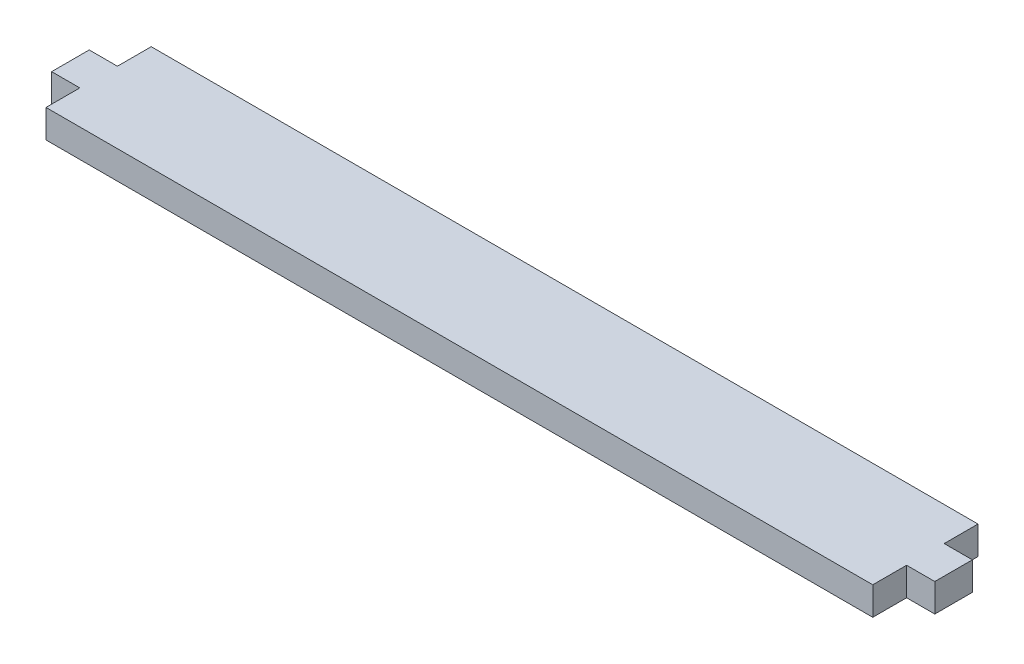
SolidWorks part; units mm, degrees
ref_plane "Front Plane" through (0, 0, 0) normal (0, 0, 1) x (1, 0, 0)
ref_plane "Top Plane" through (0, 0, 0) normal (0, 1, 0) x (1, 0, 0)
ref_plane "Right Plane" through (0, 0, 0) normal (1, 0, 0) x (0, 0, -1)
sketch "Sketch1" plane through (0, 0, 0) normal (0, 1, 0) x (1, 0, 0)
  line L1 (139.7, -17.78) -> (-139.7, -17.78)
  line L2 (139.7, -17.78) -> (139.7, 17.78)
  line L3 (139.7, 17.78) -> (-139.7, 17.78)
  line L4 (-139.7, -17.78) -> (-139.7, 17.78)
  line L5 (139.7, -17.78) -> (-139.7, 17.78) construction
  line L6 (139.7, 17.78) -> (-139.7, -17.78) construction
  point P0 (0, 0)
  dimension "D1" = 279.4
  dimension "D2" = 35.56
extrude "Boss-Extrude1" add sketch "Sketch1" along normal blind 9.525
sketch "Sketch2" plane through (139.7, 0, 0) normal (1, 0, 0) x (0, 0, -1)
  line L0 (-17.78, 0) -> (17.78, 0) construction
  line L1 (-6.35, 0) -> (6.35, 0)
  line L2 (-6.35, 0) -> (-6.35, 9.525)
  line L3 (-6.35, 9.525) -> (6.35, 9.525)
  line L4 (6.35, 0) -> (6.35, 9.525)
  line L5 (-17.78, 9.525) -> (17.78, 9.525) construction
  line L6 (-17.78, 9.525) -> (-17.78, 0) construction
  dimension "D1" = 12.7
  dimension "D2" = 11.43
extrude "Boss-Extrude2" add sketch "Sketch2" along normal blind 9.525
mirror "Mirror1" about plane through (0, 0, 0) normal (1, 0, 0) of "Boss-Extrude2"
sketch "Sketch3" plane through (0, 0, 0) normal (0, -1, 0) x (1, 0, 0)
  line L0 (-138.2612, -11.4174) -> (137.3788, -11.4174)
